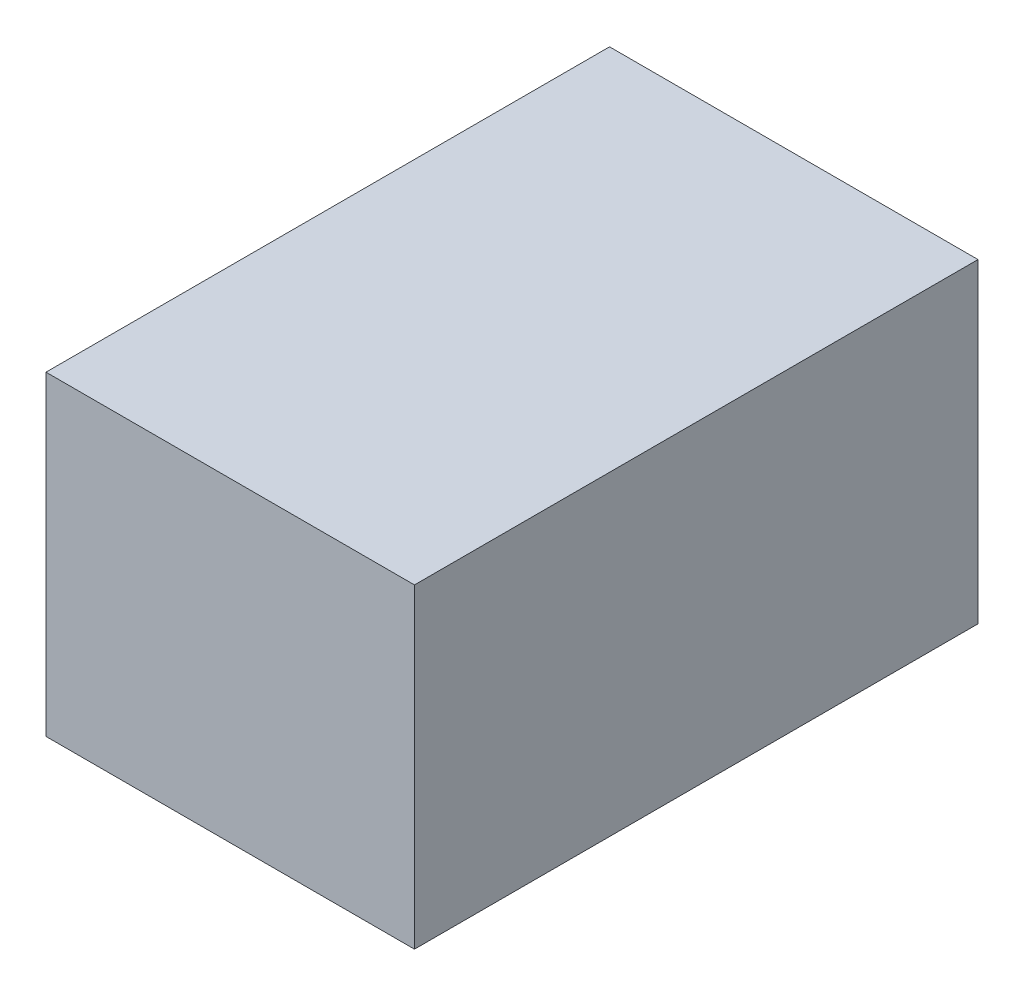
SolidWorks part; units mm, degrees
ref_plane "Front Plane" through (0, 0, 0) normal (0, 0, 1) x (1, 0, 0)
ref_plane "Top Plane" through (0, 0, 0) normal (0, 1, 0) x (1, 0, 0)
ref_plane "Right Plane" through (0, 0, 0) normal (1, 0, 0) x (0, 0, -1)
sketch "Sketch1" plane through (0, 0, 0) normal (0, 1, 0) x (1, 0, 0)
  line L1 (-1470.2455, -349.5689) -> (-1393.7455, -349.5689)
  line L2 (-1470.2455, -349.5689) -> (-1470.2455, -232.5689)
  line L3 (-1470.2455, -232.5689) -> (-1393.7455, -232.5689)
  line L4 (-1393.7455, -349.5689) -> (-1393.7455, -232.5689)
  dimension "D1" = 117
  dimension "D2" = 76.5
extrude "Boss-Extrude1" add sketch "Sketch1" along normal blind 65.5
